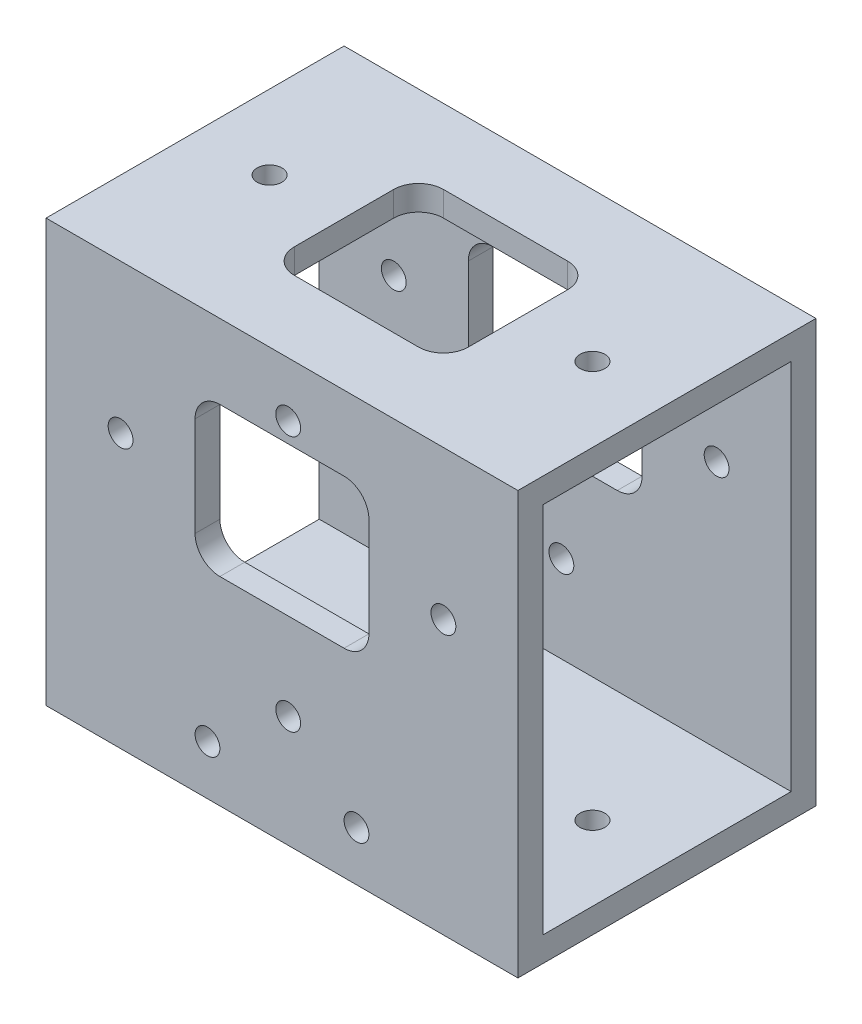
SolidWorks part; units mm, degrees
material "1060 Alloy"
ref_plane "Front Plane" through (0, 0, 0) normal (0, 0, 1) x (1, 0, 0)
ref_plane "Top Plane" through (0, 0, 0) normal (0, 1, 0) x (1, 0, 0)
ref_plane "Right Plane" through (0, 0, 0) normal (1, 0, 0) x (0, 0, -1)
sketch "Sketch1" plane through (0, 0, 0) normal (0, 1, 0) x (1, 0, 0)
  line L1 (-95, -60) -> (95, -60)
  line L2 (-95, -60) -> (-95, 60)
  line L3 (-95, 60) -> (95, 60)
  line L4 (95, -60) -> (95, 60)
  line L5 (-95, -60) -> (95, 60) construction
  line L6 (-95, 60) -> (95, -60) construction
  point P0 (0, 0)
extrude "Boss-Extrude1" add sketch "Sketch1" along normal blind 170
ref_plane "Plane1" through (95, 0, 0) normal (1, 0, 0) x (0, 0, -1)
sketch "Sketch2" plane through (95, 0, 0) normal (1, 0, 0) x (0, 0, -1)
  line L0 (-60, 85) -> (60, 85)
  line L3 (0, 170) -> (0, 0)
  line L4 (-60, 170) -> (60, 170) construction
  line L5 (-60, 170) -> (-60, 0) construction
  line L6 (60, 170) -> (60, 0) construction
  line L8 (-50, 10) -> (50, 10)
  line L9 (-50, 10) -> (-50, 160)
  line L10 (-50, 160) -> (50, 160)
  line L11 (50, 10) -> (50, 160)
  line L12 (-50, 10) -> (50, 160) construction
  line L13 (-50, 160) -> (50, 10) construction
  point P11 (0, 85)
  dimension "D1" = 10
  dimension "D2" = 10
extrude "Cut-Extrude1" cut sketch "Sketch2" against normal blind 190 contours L10 L9 L0 L3 | L0 L11 L10 L3 | L8 L11 L0 L3 | L9 L8 L3 L0
ref_plane "Plane2" through (0, 0, 60) normal (0, 0, 1) x (1, 0, 0)
sketch "Sketch3" plane through (0, 0, 60) normal (0, 0, 1) x (1, 0, 0)
  line L0 (95, 170) -> (95, 0) construction
  line L1 (-25, 80) -> (25, 80)
  line L2 (-35, 90) -> (-35, 130)
  line L3 (-25, 140) -> (25, 140)
  line L4 (35, 90) -> (35, 130)
  line L5 (-95, 170) -> (-95, 0) construction
  line L7 (95, 170) -> (-95, 170) construction
  arc A0 (35, 130) -> (25, 140) centre (25, 130) ccw
  arc A1 (-35, 130) -> (-25, 140) centre (-25, 130) cw
  arc A2 (-35, 90) -> (-25, 80) centre (-25, 90) ccw
  arc A3 (25, 80) -> (35, 90) centre (25, 90) ccw
  point P8 (0, 170)
  point P14 (35, 140)
  point P17 (-35, 140)
  point P20 (-35, 80)
  dimension "D5" = 10
  dimension "D6" = 10
  dimension "D1" = 60
  dimension "D2" = 60
  dimension "D3" = 30
  dimension "D4" = 60
extrude "Cut-Extrude2" cut sketch "Sketch3" against normal blind 15
ref_plane "Plane3" through (0, 0, -60) normal (0, 0, -1) x (-1, 0, 0)
sketch "Sketch4" plane through (0, 0, -60) normal (0, 0, -1) x (-1, 0, 0)
  line L0 (95, 170) -> (95, 0) construction
  line L1 (-25, 80) -> (25, 80)
  line L2 (-35, 90) -> (-35, 130)
  line L3 (-25, 140) -> (25, 140)
  line L4 (35, 90) -> (35, 130)
  line L5 (-95, 170) -> (-95, 0) construction
  line L6 (-95, 170) -> (95, 170) construction
  arc A0 (-35, 130) -> (-25, 140) centre (-25, 130) cw
  arc A1 (-35, 90) -> (-25, 80) centre (-25, 90) ccw
  arc A2 (25, 80) -> (35, 90) centre (25, 90) ccw
  arc A3 (35, 130) -> (25, 140) centre (25, 130) ccw
  point P14 (-35, 80)
  point P17 (35, 80)
  point P20 (35, 140)
  dimension "D5" = 10
  dimension "D1" = 60
  dimension "D2" = 60
  dimension "D3" = 60
  dimension "D4" = 30
extrude "Cut-Extrude3" cut sketch "Sketch4" against normal blind 15
ref_plane "Plane4" through (0, 170, 0) normal (0, 1, 0) x (1, 0, 0)
sketch "Sketch5" plane through (0, 170, 0) normal (0, 1, 0) x (1, 0, 0)
  line L0 (95, -60) -> (95, 60) construction
  line L1 (-25, -30) -> (25, -30)
  line L2 (-35, -20) -> (-35, 20)
  line L3 (-25, 30) -> (25, 30)
  line L4 (35, -20) -> (35, 20)
  line L5 (-95, 60) -> (-95, -60) construction
  line L6 (95, 60) -> (-95, 60) construction
  line L7 (-95, -60) -> (95, -60) construction
  arc A0 (-35, 20) -> (-25, 30) centre (-25, 20) cw
  arc A1 (-25, -30) -> (-35, -20) centre (-25, -20) cw
  arc A2 (35, -20) -> (25, -30) centre (25, -20) cw
  arc A3 (35, 20) -> (25, 30) centre (25, 20) ccw
  point P14 (-35, 30)
  point P17 (-35, -30)
  point P22 (35, 30)
  dimension "D5" = 10
  dimension "D1" = 60
  dimension "D2" = 60
  dimension "D3" = 30
  dimension "D4" = 30
extrude "Cut-Extrude4" cut sketch "Sketch5" against normal blind 15
ref_plane "Plane5" through (0, 0, -70) normal (0, 0, -1) x (-1, 0, 0)
sketch "Sketch6" plane through (0, 0, -70) normal (0, 0, -1) x (-1, 0, 0)
  line L0 (95, 170) -> (95, 0) construction
  line L1 (-95, 170) -> (-95, 0) construction
  line L2 (-95, 0) -> (95, 0) construction
  line L3 (-95, 170) -> (95, 170) construction
  point P0 (65, 110)
  point P1 (-65, 110)
  point P2 (-2.5, 45)
  dimension "D1" = 30
  dimension "D2" = 30
  dimension "D3" = 45
  dimension "D4" = 60
  dimension "D5" = 60
  dimension "D6" = 92.5
hole_wizard "M10x1.0 Tapped Hole1" positions "3DSketch1" profile "Sketch7" tap size "M10x1.0" standard "ANSI Metric"
sketch3d "3DSketch1"
  point P0 (65, 110, -70)
  point P3 (-65, 110, -70)
  point P6 (2.5, 45, -70)
sketch "Sketch7" plane through (65, 110, -70) normal (1, 0, 0) x (0, 1, 0)
  line L0 (0, 0) -> (0, 25.7039)
  line L1 (0, 25.7039) -> (4.5, 23)
  line L2 (4.5, 23) -> (4.5, 20)
  line L3 (4.5, 20) -> (5, 20)
  line L4 (5, 20) -> (5, 0)
  line L5 (5, 0) -> (0, 0)
  line L10 (0, 25.7039) -> (-4.5, 23) construction
  line L11 (0, -6.35) -> (0, 107.95) construction
  dimension "Tap Drill Dia." = 9
  dimension "Tap Drill Depth" = 23
  dimension "Thread Major Dia." = 10
  dimension "Thread Depth" = 20
  dimension "Drill Angle" = 118
ref_plane "Plane6" through (0, 170, 0) normal (0, 1, 0) x (1, 0, 0)
sketch "Sketch8" plane through (0, 170, 0) normal (0, 1, 0) x (1, 0, 0)
  line L0 (-95, 60) -> (-95, -60) construction
  line L1 (95, -60) -> (95, 60) construction
  line L2 (-95, -60) -> (95, -60) construction
  point P0 (-65, 0)
  point P1 (65, 0)
  dimension "D1" = 30
  dimension "D2" = 30
  dimension "D3" = 60
  dimension "D4" = 60
hole_wizard "M10x1.0 Tapped Hole2" positions "3DSketch2" profile "Sketch9" tap size "M10x1.0" standard "ANSI Metric"
sketch3d "3DSketch2"
  point P0 (-65, 170, 0)
  point P3 (65, 170, 0)
sketch "Sketch9" plane through (-65, 170, 0) normal (1, 0, 0) x (0, 0, 1)
  line L0 (0, 0) -> (0, 25.7039)
  line L1 (0, 25.7039) -> (4.5, 23)
  line L2 (4.5, 23) -> (4.5, 20)
  line L3 (4.5, 20) -> (5, 20)
  line L4 (5, 20) -> (5, 0)
  line L5 (5, 0) -> (0, 0)
  line L10 (0, 25.7039) -> (-4.5, 23) construction
  line L11 (0, -6.35) -> (0, 107.95) construction
  dimension "Tap Drill Dia." = 9
  dimension "Tap Drill Depth" = 23
  dimension "Thread Major Dia." = 10
  dimension "Thread Depth" = 20
  dimension "Drill Angle" = 118
ref_plane "Plane7" through (0, 0, 60) normal (0, 0, 1) x (1, 0, 0)
sketch "Sketch10" plane through (0, 0, 60) normal (0, 0, 1) x (1, 0, 0)
  line L0 (95, 170) -> (95, 0) construction
  line L1 (25, 140) -> (-25, 140) construction
  line L2 (-95, 0) -> (95, 0) construction
  line L3 (-95, 170) -> (-95, 0) construction
  point P0 (-65, 110)
  point P1 (65, 110)
  point P3 (2.5, 45)
  point P5 (2.5, 148)
  point P11 (-30, 20)
  point P12 (30, 20)
  dimension "D1" = 92.5
  dimension "D2" = 8
  dimension "D3" = 20
  dimension "D4" = 20
  dimension "D5" = 65
  dimension "D6" = 65
hole_wizard "M10x1.0 Tapped Hole3" positions "3DSketch5" profile "Sketch13" tap size "M10x1.0" standard "ANSI Metric"
sketch3d "3DSketch5"
  point P0 (-65, 110, 60)
  point P3 (65, 110, 60)
  point P6 (2.5, 45, 60)
  point P9 (2.5, 148, 60)
sketch "Sketch13" plane through (-65, 110, 60) normal (1, 0, 0) x (0, -1, 0)
  line L0 (0, 0) -> (0, 25.7039)
  line L1 (0, 25.7039) -> (4.5, 23)
  line L2 (4.5, 23) -> (4.5, 20)
  line L3 (4.5, 20) -> (5, 20)
  line L4 (5, 20) -> (5, 0)
  line L5 (5, 0) -> (0, 0)
  line L10 (0, 25.7039) -> (-4.5, 23) construction
  line L11 (0, -6.35) -> (0, 107.95) construction
  dimension "Tap Drill Dia." = 9
  dimension "Tap Drill Depth" = 23
  dimension "Thread Major Dia." = 10
  dimension "Thread Depth" = 20
  dimension "Drill Angle" = 118
ref_plane "Plane8" through (0, 0, 0) normal (0, -1, 0) x (-1, 0, 0)
sketch "Sketch14" plane through (0, 0, 0) normal (0, -1, 0) x (-1, 0, 0)
  point P0 (-65, 0)
  point P1 (65, 0)
hole_wizard "M10x1.0 Tapped Hole4" positions "3DSketch6" profile "Sketch15" tap size "M10x1.0" standard "ANSI Metric"
sketch3d "3DSketch6"
  point P0 (65, 0, 0)
  point P3 (-65, 0, 0)
sketch "Sketch15" plane through (65, 0, 0) normal (1, 0, 0) x (0, 0, -1)
  line L0 (0, 0) -> (0, 25.7039)
  line L1 (0, 25.7039) -> (4.5, 23)
  line L2 (4.5, 23) -> (4.5, 20)
  line L3 (4.5, 20) -> (5, 20)
  line L4 (5, 20) -> (5, 0)
  line L5 (5, 0) -> (0, 0)
  line L10 (0, 25.7039) -> (-4.5, 23) construction
  line L11 (0, -6.35) -> (0, 107.95) construction
  dimension "Tap Drill Dia." = 9
  dimension "Tap Drill Depth" = 23
  dimension "Thread Major Dia." = 10
  dimension "Thread Depth" = 20
  dimension "Drill Angle" = 118
hole_wizard "M10x1.0 Tapped Hole5" positions "3DSketch7" profile "Sketch16" tap size "M10x1.0" standard "ANSI Metric"
sketch3d "3DSketch7"
  point P0 (-30, 20, 60)
  point P3 (30, 20, 60)
sketch "Sketch16" plane through (-30, 20, 60) normal (1, 0, 0) x (0, -1, 0)
  line L0 (0, 0) -> (0, 25.7039)
  line L1 (0, 25.7039) -> (4.5, 23)
  line L2 (4.5, 23) -> (4.5, 20)
  line L3 (4.5, 20) -> (5, 20)
  line L4 (5, 20) -> (5, 0)
  line L5 (5, 0) -> (0, 0)
  line L10 (0, 25.7039) -> (-4.5, 23) construction
  line L11 (0, -6.35) -> (0, 107.95) construction
  dimension "Tap Drill Dia." = 9
  dimension "Tap Drill Depth" = 23
  dimension "Thread Major Dia." = 10
  dimension "Thread Depth" = 20
  dimension "Drill Angle" = 118
